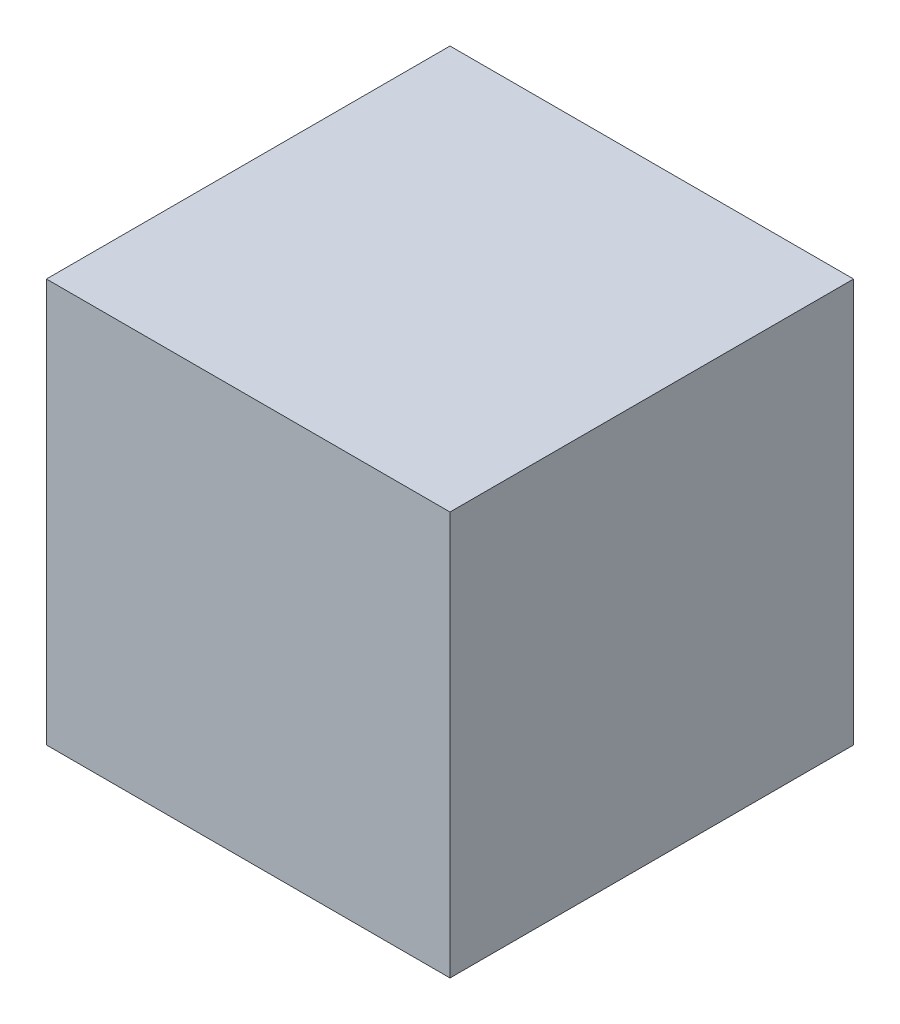
SolidWorks part; units mm, degrees
ref_plane "Alzado" through (0, 0, 0) normal (0, 0, 1) x (1, 0, 0)
ref_plane "Planta" through (0, 0, 0) normal (0, 1, 0) x (1, 0, 0)
ref_plane "Vista lateral" through (0, 0, 0) normal (1, 0, 0) x (0, 0, -1)
sketch "Croquis1" plane through (0, 0, 0) normal (0, 1, 0) x (1, 0, 0)
  line L1 (-15, 15) -> (15, 15)
  line L2 (-15, 15) -> (-15, -15)
  line L3 (-15, -15) -> (15, -15)
  line L4 (15, 15) -> (15, -15)
  line L5 (-15, 15) -> (15, -15) construction
  line L6 (-15, -15) -> (15, 15) construction
  point P0 (0, 0)
  dimension "D1" = 30
  dimension "D2" = 30
extrude "Saliente-Extruir1" add sketch "Croquis1" along normal blind 30
